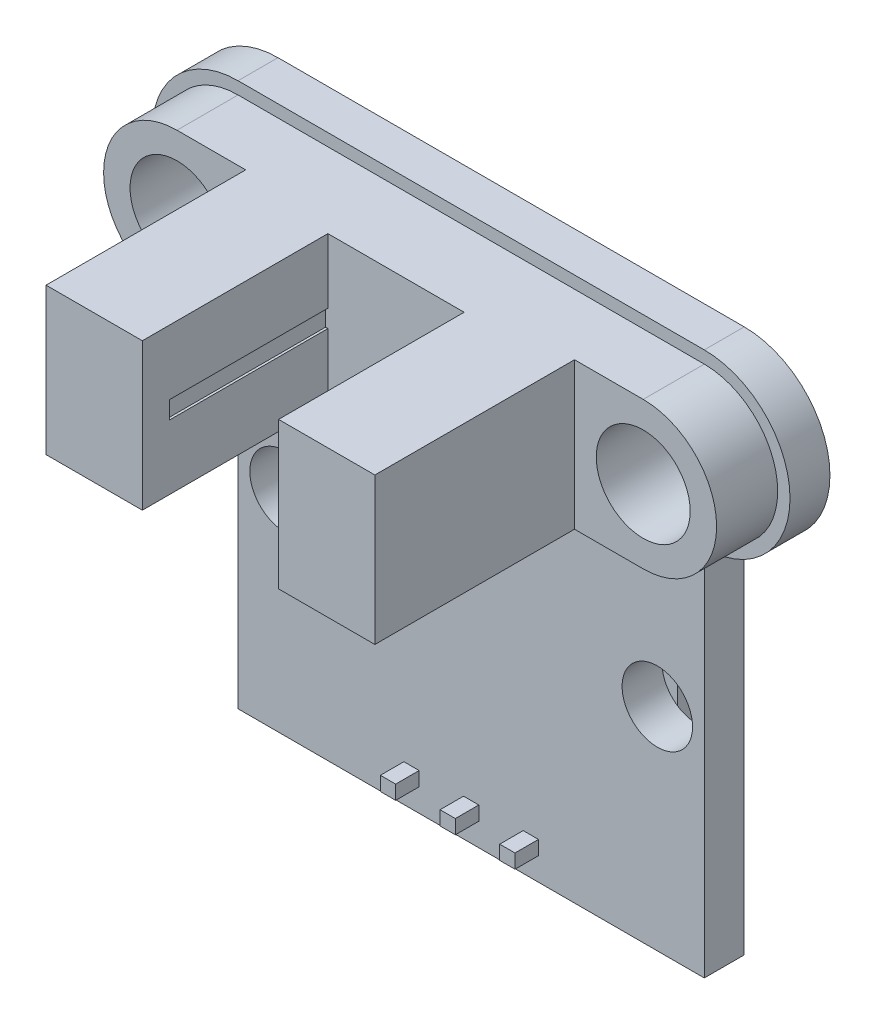
SolidWorks part; units mm, degrees
ref_plane "Ön Düzlem" through (0, 0, 0) normal (0, 0, 1) x (1, 0, 0)
ref_plane "Üst Düzlem" through (0, 0, 0) normal (0, 1, 0) x (1, 0, 0)
ref_plane "Sağ Düzlem" through (0, 0, 0) normal (1, 0, 0) x (0, 0, -1)
sketch "Çizim1" plane through (0, 0, 0) normal (0, 0, 1) x (1, 0, 0)
  line L0 (9.925, -11.575) -> (7.925, -11.575) construction
  line L1 (-9.925, -11.575) -> (9.925, -11.575)
  line L2 (-9.925, -11.575) -> (-9.925, 4.275)
  line L3 (-9.925, 11.575) -> (9.925, 11.575)
  line L4 (9.925, -11.575) -> (9.925, 4.275)
  line L5 (7.925, -11.575) -> (7.925, -2.575) construction
  line L9 (0, 11.575) -> (0, -11.575) construction
  arc A0 (9.925, 4.275) -> (9.925, 11.575) centre (9.925, 7.925) ccw
  circle A1 centre (9.925, 7.925) radius 2
  circle A2 centre (-9.925, 7.925) radius 2
  arc A3 (-9.925, 4.275) -> (-9.925, 11.575) centre (-9.925, 7.925) cw
  circle A4 centre (7.925, -2.575) radius 1.5
  circle A5 centre (-7.925, -2.575) radius 1.5
  point P0 (0, 0)
extrude "Yükseklik-Ekstrüzyon1" add sketch "Çizim1" along normal blind 1.7
sketch "Çizim2" plane through (0, 0, 1.7) normal (0, 0, 1) x (1, 0, 0)
  line L0 (-9.925, 11.05) -> (9.925, 11.05)
  line L1 (9.925, 4.8) -> (-9.925, 4.8)
  arc A0 (9.925, 4.8) -> (9.925, 11.05) centre (9.925, 7.925) ccw
  arc A1 (-9.925, 11.05) -> (-9.925, 4.8) centre (-9.925, 7.925) ccw
  circle A2 centre (-9.925, 7.925) radius 2
  circle A3 centre (9.925, 7.925) radius 2
extrude "Yükseklik-Ekstrüzyon2" add sketch "Çizim2" along normal blind 2.6
sketch "Çizim3" plane through (0, 0, 4.3) normal (0, 0, 1) x (1, 0, 0)
  line L2 (-9.925, 4.8) -> (9.925, 4.8) construction
  line L3 (2.9, 4.8) -> (7.0001, 4.8)
  line L4 (-7.0001, 11.05) -> (-2.9, 11.05)
  line L5 (-7.0001, 11.05) -> (-7.0001, 4.8)
  line L6 (-7.0001, 4.8) -> (-2.9, 4.8)
  line L7 (7.0001, 11.05) -> (7.0001, 4.8)
  line L11 (-2.9, 11.05) -> (-2.9, 4.8)
  line L13 (2.9, 11.05) -> (2.9, 4.8)
  line L18 (2.9, 11.05) -> (7.0001, 11.05)
  point P6 (0, 7.925)
  point P11 (0, 7.925)
  dimension "D1" = 5.8
extrude "Yükseklik-Ekstrüzyon3" add sketch "Çizim3" along normal blind 8.5
sketch "Çizim4" plane through (0, 0, 4.3) normal (0, 0, 1) x (1, 0, 0)
  line L4 (2.9, 11.05) -> (-2.9, 11.05)
  line L5 (-2.9, 11.05) -> (-2.9, 4.8)
  line L6 (-2.9, 4.8) -> (2.9, 4.8)
  line L7 (2.9, 4.8) -> (2.9, 11.05)
  line L8 (2.9, 11.05) -> (-2.9, 11.05)
  line L9 (-2.9, 11.05) -> (-2.9, 4.8)
  line L10 (-2.9, 4.8) -> (2.9, 4.8)
  line L11 (2.9, 4.8) -> (2.9, 11.05)
  dimension "D1" = 0
extrude "Yükseklik-Ekstrüzyon4" add sketch "Çizim4" along normal blind 0.6
sketch "Çizim5" plane through (0, 0, 0) normal (0, 0, -1) x (-1, 0, 0)
  line L0 (9.925, -11.575) -> (-9.925, -11.575) construction
  line L5 (0, -11.575) -> (0, -9.035) construction
  line L6 (1.02, -9.035) -> (1.27, -9.285)
  line L8 (-1.02, -9.035) -> (1.02, -9.035)
  line L9 (-1.27, -9.285) -> (-1.27, -11.325)
  line L10 (-1.02, -11.575) -> (1.02, -11.575)
  line L11 (1.27, -9.285) -> (1.27, -11.325)
  line L12 (-1.27, -9.035) -> (1.27, -11.575) construction
  line L13 (-1.27, -11.575) -> (1.27, -9.035) construction
  line L14 (1.02, -11.575) -> (1.27, -11.325)
  line L15 (-1.27, -11.325) -> (-1.02, -11.575)
  line L16 (-1.27, -9.285) -> (-1.02, -9.035)
  line L17 (-1.52, -11.575) -> (-3.56, -11.575)
  line L18 (-3.56, -11.575) -> (-3.81, -11.325)
  line L19 (-3.81, -9.285) -> (-3.81, -11.325)
  line L20 (-3.56, -9.035) -> (-3.81, -9.285)
  line L21 (-1.52, -9.035) -> (-3.56, -9.035)
  line L22 (-1.27, -11.325) -> (-1.52, -11.575)
  line L23 (-1.27, -9.285) -> (-1.52, -9.035)
  line L24 (3.56, -11.575) -> (1.52, -11.575)
  line L25 (1.52, -11.575) -> (1.27, -11.325)
  line L26 (1.52, -9.035) -> (1.27, -9.285)
  line L27 (3.56, -9.035) -> (1.52, -9.035)
  line L28 (3.81, -11.325) -> (3.56, -11.575)
  line L29 (3.81, -9.285) -> (3.56, -9.035)
  line L30 (3.81, -9.285) -> (3.81, -11.325)
  point P0 (0, -11.575)
  point P3 (0, -10.305)
  line M15 (-9.925, -11.575) -> (9.925, -11.575)
extrude "Yükseklik-Ekstrüzyon6" add sketch "Çizim5" along normal blind 2.54 contours L9 L23 L21 L20 L19 L18 L22 M15 | L16 L9 L15 L14 L11 L6 L8 M15 | L30 L29 L27 L26 L11 L25 L28 M15
sketch "Çizim6" plane through (0, -11.575, 0) normal (0, -1, 0) x (1, 0, 0)
  line L1 (-9.925, 1.7) -> (9.925, 1.7)
  line L2 (-9.925, 1.7) -> (-9.925, 0)
  line L3 (-9.925, 0) -> (9.925, 0)
  line L4 (9.925, 1.7) -> (9.925, 0)
extrude "Yükseklik-Ekstrüzyon7" add sketch "Çizim6" along normal blind 0.01
sketch "Çizim7" plane through (2.9, 0, 0) normal (-1, 0, 0) x (0, 0, 1)
  line L0 (4.9, 7.925) -> (11.65, 7.925) construction
  line L1 (4.9, 4.8) -> (4.9, 11.05) construction
  line L3 (4.9, 8.3) -> (11.65, 8.3)
  line L4 (4.9, 8.3) -> (4.9, 7.55)
  line L5 (4.9, 7.55) -> (11.65, 7.55)
  line L6 (11.65, 8.3) -> (11.65, 7.55)
  line L7 (4.9, 8.3) -> (11.65, 7.55) construction
  line L8 (4.9, 7.55) -> (11.65, 8.3) construction
  point P4 (8.275, 7.925)
extrude "Kes-Ekstrüzyon1" cut sketch "Çizim7" against normal blind 0.1 and the other way blind 5.9
sketch "Çizim8" plane through (0, 0, -2.54) normal (0, 0, -1) x (-1, 0, 0)
  line L0 (-1.27, -9.285) -> (-1.27, -11.325) construction
  line L3 (1.27, -9.285) -> (1.27, -11.325) construction
  line L4 (1.145, -11.45) -> (-1.145, -9.16) construction
  line L5 (1.02, -11.575) -> (1.27, -11.325) construction
  line L6 (-1.27, -9.285) -> (-1.02, -9.035) construction
  line L7 (2.8725, -9.9725) -> (2.2075, -9.9725)
  line L8 (-0.3325, -10.6375) -> (0.3325, -10.6375)
  line L9 (-0.3325, -10.6375) -> (-0.3325, -9.9725)
  line L10 (-0.3325, -9.9725) -> (0.3325, -9.9725)
  line L11 (0.3325, -10.6375) -> (0.3325, -9.9725)
  line L12 (-0.3325, -10.6375) -> (0.3325, -9.9725) construction
  line L13 (-0.3325, -9.9725) -> (0.3325, -10.6375) construction
  line L14 (2.2075, -10.6375) -> (2.2075, -9.9725)
  line L15 (2.8725, -10.6375) -> (2.2075, -10.6375)
  line L16 (2.8725, -10.6375) -> (2.8725, -9.9725)
  line L17 (-2.2075, -9.9725) -> (-2.8725, -9.9725)
  line L18 (-2.8725, -10.6375) -> (-2.8725, -9.9725)
  line L19 (-2.2075, -10.6375) -> (-2.8725, -10.6375)
  line L20 (-2.2075, -10.6375) -> (-2.2075, -9.9725)
  point P14 (0, -10.305)
ref_plane "Düzlem1" through (0, 0, 0) normal (1, 0, 0) x (0, 0, -1)
sketch "Çizim9" plane through (0, 0, 0) normal (1, 0, 0) x (0, 0, -1)
  line L0 (2.54, -10.305) -> (4.04, -10.305)
  line L1 (4.54, -9.805) -> (4.54, -3.305)
  arc A0 (4.04, -10.305) -> (4.54, -9.805) centre (4.04, -9.805) ccw
  dimension "D1" = 0.5
sweep "Süpür1" add profiles "Çizim8" path "Çizim9"
sketch "Çizim10" plane through (0, 0, -2.54) normal (0, 0, -1) x (-1, 0, 0)
  line L20 (-1.52, -11.575) -> (-1.27, -11.325)
  line L21 (-1.27, -11.325) -> (-1.02, -11.575)
  line L22 (-1.02, -11.575) -> (1.02, -11.575)
  line L23 (1.02, -11.575) -> (1.27, -11.325)
  line L24 (1.27, -11.325) -> (1.52, -11.575)
  line L25 (1.52, -11.575) -> (3.56, -11.575)
  line L26 (3.56, -11.575) -> (3.81, -11.325)
  line L27 (3.81, -11.325) -> (3.81, -9.285)
  line L28 (3.81, -9.285) -> (3.56, -9.035)
  line L29 (3.56, -9.035) -> (1.52, -9.035)
  line L30 (1.52, -9.035) -> (1.27, -9.285)
  line L31 (1.27, -9.285) -> (1.02, -9.035)
  line L32 (1.02, -9.035) -> (-1.02, -9.035)
  line L33 (-1.02, -9.035) -> (-1.27, -9.285)
  line L34 (-1.27, -9.285) -> (-1.52, -9.035)
  line L35 (-1.52, -9.035) -> (-3.56, -9.035)
  line L36 (-3.56, -9.035) -> (-3.81, -9.285)
  line L37 (-3.81, -9.285) -> (-3.81, -11.325)
  line L38 (-3.81, -11.325) -> (-3.56, -11.575)
  line L39 (-3.56, -11.575) -> (-1.52, -11.575)
  line L40 (-1.52, -11.575) -> (-1.27, -11.325)
  line L41 (-1.27, -11.325) -> (-1.02, -11.575)
  line L42 (-1.02, -11.575) -> (1.02, -11.575)
  line L43 (1.02, -11.575) -> (1.27, -11.325)
  line L44 (1.27, -11.325) -> (1.52, -11.575)
  line L45 (1.52, -11.575) -> (3.56, -11.575)
  line L46 (3.56, -11.575) -> (3.81, -11.325)
  line L47 (3.81, -11.325) -> (3.81, -9.285)
  line L48 (3.81, -9.285) -> (3.56, -9.035)
  line L49 (3.56, -9.035) -> (1.52, -9.035)
  line L50 (1.52, -9.035) -> (1.27, -9.285)
  line L51 (1.27, -9.285) -> (1.02, -9.035)
  line L52 (1.02, -9.035) -> (-1.02, -9.035)
  line L53 (-1.02, -9.035) -> (-1.27, -9.285)
  line L54 (-1.27, -9.285) -> (-1.52, -9.035)
  line L55 (-1.52, -9.035) -> (-3.56, -9.035)
  line L56 (-3.56, -9.035) -> (-3.81, -9.285)
  line L57 (-3.81, -9.285) -> (-3.81, -11.325)
  line L58 (-3.81, -11.325) -> (-3.56, -11.575)
  line L59 (-3.56, -11.575) -> (-1.52, -11.575)
  dimension "D1" = 0
sketch "Çizim11" plane through (0, 0, 1.7) normal (0, 0, 1) x (1, 0, 0)
  line L0 (-1.27, -9.285) -> (-1.27, -11.325) construction
  line L1 (0, -9.035) -> (0, -11.575) construction
  line L2 (-1.02, -9.035) -> (1.02, -9.035) construction
  line L3 (1.02, -11.575) -> (-1.02, -11.575) construction
  line L4 (1.27, -9.285) -> (1.27, -11.325) construction
  line L5 (-2.215, -10.605) -> (-2.865, -10.605)
  line L6 (-0.325, -10.005) -> (0.325, -10.005)
  line L7 (-0.325, -10.005) -> (-0.325, -10.605)
  line L8 (-0.325, -10.605) -> (0.325, -10.605)
  line L9 (0.325, -10.005) -> (0.325, -10.605)
  line L10 (-0.325, -10.005) -> (0.325, -10.605) construction
  line L11 (-0.325, -10.605) -> (0.325, -10.005) construction
  line L12 (-2.865, -10.005) -> (-2.865, -10.605)
  line L13 (-2.215, -10.005) -> (-2.865, -10.005)
  line L14 (-2.215, -10.005) -> (-2.215, -10.605)
  line L15 (2.865, -10.605) -> (2.215, -10.605)
  line L16 (2.215, -10.005) -> (2.215, -10.605)
  line L17 (2.865, -10.005) -> (2.215, -10.005)
  line L18 (2.865, -10.005) -> (2.865, -10.605)
  point P14 (0, -10.305)
extrude "Yükseklik-Ekstrüzyon8" add sketch "Çizim11" along normal blind 1
sketch "Çizim12" plane through (0, 0, 0) normal (0, 0, -1) x (-1, 0, 0)
  line L0 (-9.925, -2.575) -> (-3.925, -2.575) construction
  line L1 (-9.925, -11.585) -> (-9.925, 4.275) construction
  line L2 (-3.925, -2.575) -> (-3.925, -0.075)
  line L3 (-3.925, -0.075) -> (-0.175, -0.075)
  line L4 (-0.175, -0.075) -> (-0.175, -5.075)
  line L5 (-0.175, -5.075) -> (-3.925, -5.075)
  line L6 (-3.925, -5.075) -> (-3.925, -2.575)
extrude "Yükseklik-Ekstrüzyon9" add sketch "Çizim12" along normal blind 1.5
